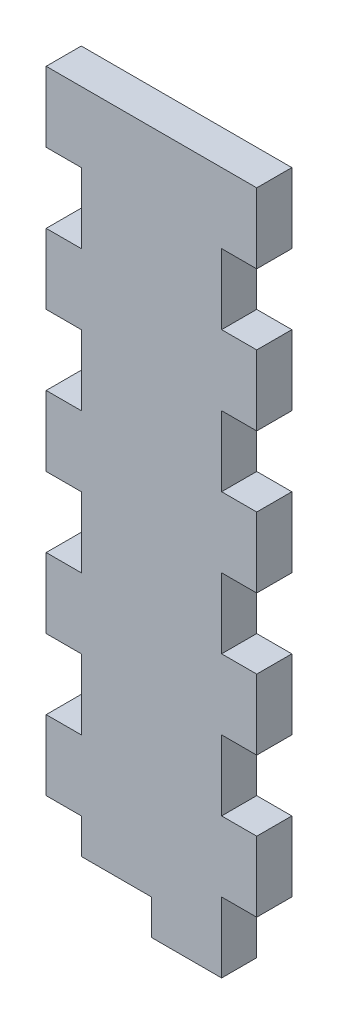
SolidWorks part; units mm, degrees
ref_plane "Front Plane" through (0, 0, 0) normal (0, 0, 1) x (1, 0, 0)
ref_plane "Top Plane" through (0, 0, 0) normal (0, 1, 0) x (1, 0, 0)
ref_plane "Right Plane" through (0, 0, 0) normal (1, 0, 0) x (0, 0, -1)
sketch "Sketch1" plane through (0, 0, 0) normal (0, 0, 1) x (1, 0, 0)
  line L1 (0, 0) -> (38.1, 0)
  line L2 (0, 0) -> (0, 127)
  line L3 (0, 127) -> (38.1, 127)
  line L4 (38.1, 0) -> (38.1, 127)
  dimension "D1" = 38.1
  dimension "D2" = 127
extrude "Boss-Extrude1" add sketch "Sketch1" along normal blind 6.35 contours L2 L3 L4 L1
sketch "Sketch2" plane through (0, 0, 6.35) normal (0, 0, 1) x (1, 0, 0)
  line L1 (0, 0) -> (6.35, 0)
  line L2 (0, 0) -> (0, 12.7)
  line L3 (0, 12.7) -> (6.35, 12.7)
  line L4 (6.35, 0) -> (6.35, 12.7)
  line L5 (38.1, 0) -> (31.75, 0)
  line L6 (38.1, 0) -> (38.1, 12.7)
  line L7 (38.1, 12.7) -> (31.75, 12.7)
  line L8 (31.75, 0) -> (31.75, 12.7)
  dimension "D1" = 6.35
  dimension "D2" = 12.7
extrude "Cut-Extrude1" cut sketch "Sketch2" against normal through all
pattern_linear "LPattern1" count 6 spacing 25.4 along (0, 1, 0) of "Cut-Extrude1"
sketch "Sketch3" plane through (0, 0, 6.35) normal (0, 0, 1) x (1, 0, 0)
  line L1 (6.35, 0) -> (31.75, 0) construction
  line L2 (19.05, 0) -> (6.35, 0)
  line L3 (19.05, 0) -> (19.05, 6.35)
  line L4 (19.05, 6.35) -> (6.35, 6.35)
  line L5 (6.35, 0) -> (6.35, 6.35)
  line L6 (6.35, 0) -> (6.35, 12.7) construction
extrude "Cut-Extrude2" cut sketch "Sketch3" against normal through all
